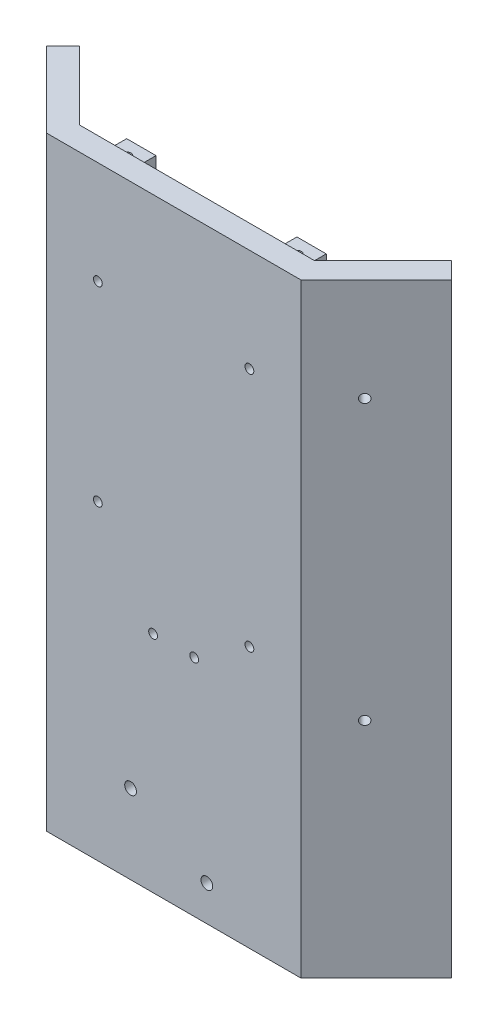
SolidWorks part; units mm, degrees
ref_plane "Front" through (0, 0, 0) normal (0, 0, 1) x (1, 0, 0)
ref_plane "Top" through (0, 0, 0) normal (0, 1, 0) x (1, 0, 0)
ref_plane "Right" through (0, 0, 0) normal (1, 0, 0) x (0, 0, -1)
sketch "Sketch1" plane through (0, 0, 0) normal (0, 1, 0) x (1, 0, 0)
  line L0 (-40, 0) -> (40, 0)
  line L1 (40, 0) -> (63.3345, 23.3345)
  line L2 (-40, 0) -> (-63.3345, 23.3345)
  line L3 (-43.3137, -8) -> (-68.9914, 17.6777)
  line L4 (-43.3137, -8) -> (43.3137, -8)
  line L5 (43.3137, -8) -> (68.9914, 17.6777)
  line L6 (-68.9914, 17.6777) -> (-63.3345, 23.3345)
  line L7 (68.9914, 17.6777) -> (63.3345, 23.3345)
  dimension "D1" = 80
  dimension "D2" = 33
  dimension "D3" = 33
  dimension "D4" = 135
  dimension "D5" = 135
  dimension "D6" = 8
extrude "Boss-Extrude1" add sketch "Sketch1" along normal blind 206
sketch "Sketch2" plane through (0, 0, 0) normal (0, 0, -1) x (-1, 0, 0)
  line L0 (-40, 206) -> (40, 206) construction
  line L1 (-34, 200) -> (-24, 200)
  line L2 (-34, 200) -> (-34, 194)
  line L3 (-34, 194) -> (-24, 194)
  line L4 (-24, 200) -> (-24, 194)
  line L5 (-34, 200) -> (-24, 194) construction
  line L6 (-34, 194) -> (-24, 200) construction
  line L7 (-40, 206) -> (-40, 0) construction
  line L8 (40, 206) -> (40, 0) construction
  line L9 (24, 200) -> (34, 200)
  line L10 (24, 200) -> (24, 194)
  line L11 (24, 194) -> (34, 194)
  line L12 (34, 200) -> (34, 194)
  line L13 (24, 200) -> (34, 194) construction
  line L14 (24, 194) -> (34, 200) construction
  point P0 (-29, 197)
  point P9 (29, 197)
  dimension "D1" = 6
  dimension "D2" = 10
  dimension "D3" = 6
  dimension "D4" = 6
  dimension "D5" = 6
  dimension "D6" = 10
  dimension "D7" = 6
  dimension "D8" = 6
extrude "Boss-Extrude2" add sketch "Sketch2" along normal blind 10
sketch "Sketch3" plane through (0, 200, 0) normal (0, 1, 0) x (1, 0, 0)
  line L0 (-34, 0) -> (-24, 10) construction
  line L1 (24, 0) -> (34, 10) construction
  circle A0 centre (-29, 5) radius 1.5
  circle A1 centre (29, 5) radius 1.5
  dimension "D1" = 3
  dimension "D2" = 3
extrude "Cut-Extrude1" cut sketch "Sketch3" against normal up to next
sketch "Sketch4" plane through (0, 0, 8) normal (0, 0, 1) x (1, 0, 0)
  line L0 (11.3137, 12) -> (-14.6671, 27) construction
  line L1 (-43.3137, 0) -> (43.3137, 0) construction
  line L2 (43.3137, 206) -> (43.3137, 0) construction
  circle A0 centre (-14.6671, 27) radius 2
  circle A1 centre (11.3137, 12) radius 2
  dimension "D2" = 4
  dimension "D3" = 4
  dimension "D1" = 30
  dimension "D4" = 12
  dimension "D5" = 30
  dimension "D6" = 32
extrude "Cut-Extrude2" cut sketch "Sketch4" against normal up to next
sketch "Sketch5" plane through (0, 0, 8) normal (0, 0, 1) x (1, 0, 0)
  line L0 (0, 0) -> (0, 76.4041) construction
  line L1 (-43.3137, 0) -> (43.3137, 0) construction
  line L2 (11.3137, 12) -> (42.9339, 66.7678) construction
  line L3 (0, 76.4041) -> (36.3731, 55.4041) construction
  line L4 (-7, 76.4041) -> (7, 76.4041) construction
  circle A0 centre (0, 76.4041) radius 2 construction
  circle A2 centre (-7, 76.4041) radius 1.5
  circle A3 centre (7, 76.4041) radius 1.5
  dimension "D2" = 4
  dimension "D4" = 50.1187
  dimension "D6" = 3
  dimension "D7" = 3
  dimension "D1" = 42
  dimension "D3" = 30
  dimension "D5" = 14
extrude "Cut-Extrude3" cut sketch "Sketch5" against normal up to next
sketch "Sketch6" plane through (0, 0, 8) normal (0, 0, 1) x (1, 0, 0)
  line L0 (-43.3137, 206) -> (43.3137, 206) construction
  line L1 (-43.3137, 206) -> (-43.3137, 0) construction
  line L2 (43.3137, 206) -> (43.3137, 0) construction
  circle A0 centre (-25.8137, 171) radius 1.5
  circle A1 centre (25.8137, 171) radius 1.5
  circle A2 centre (-25.8137, 106) radius 1.5
  circle A3 centre (25.8137, 89) radius 1.5
  dimension "D1" = 3
  dimension "D2" = 3
  dimension "D3" = 3
  dimension "D4" = 3
  dimension "D5" = 35
  dimension "D6" = 65
  dimension "D7" = 17.5
  dimension "D8" = 82
  dimension "D9" = 17.5
extrude "Cut-Extrude4" cut sketch "Sketch6" against normal up to next
sketch "Sketch7" plane through (-25.6569, 0, 25.6569) normal (-0.7071, 0, 0.7071) x (0.7071, 0, 0.7071)
  line L0 (-61.2843, 206) -> (-24.9706, 206) construction
  line L1 (-61.2843, 206) -> (-61.2843, 0) construction
  circle A0 centre (-43.4143, 171) radius 1.5
  circle A1 centre (-43.4143, 81) radius 1.5
  dimension "D1" = 3
  dimension "D2" = 3
  dimension "D3" = 35
  dimension "D4" = 90
  dimension "D5" = 17.87
extrude "Cut-Extrude5" cut sketch "Sketch7" against normal up to next
sketch "Sketch8" plane through (25.6569, 0, 25.6569) normal (0.7071, 0, 0.7071) x (0.7071, 0, -0.7071)
  line L0 (24.9706, 206) -> (61.2843, 206) construction
  line L1 (61.2843, 206) -> (61.2843, 0) construction
  circle A0 centre (40.3843, 171) radius 1.5
  circle A1 centre (40.3843, 76) radius 1.5
  dimension "D1" = 3
  dimension "D2" = 3
  dimension "D3" = 35
  dimension "D4" = 95
  dimension "D5" = 20.9
extrude "Cut-Extrude6" cut sketch "Sketch8" against normal up to next
